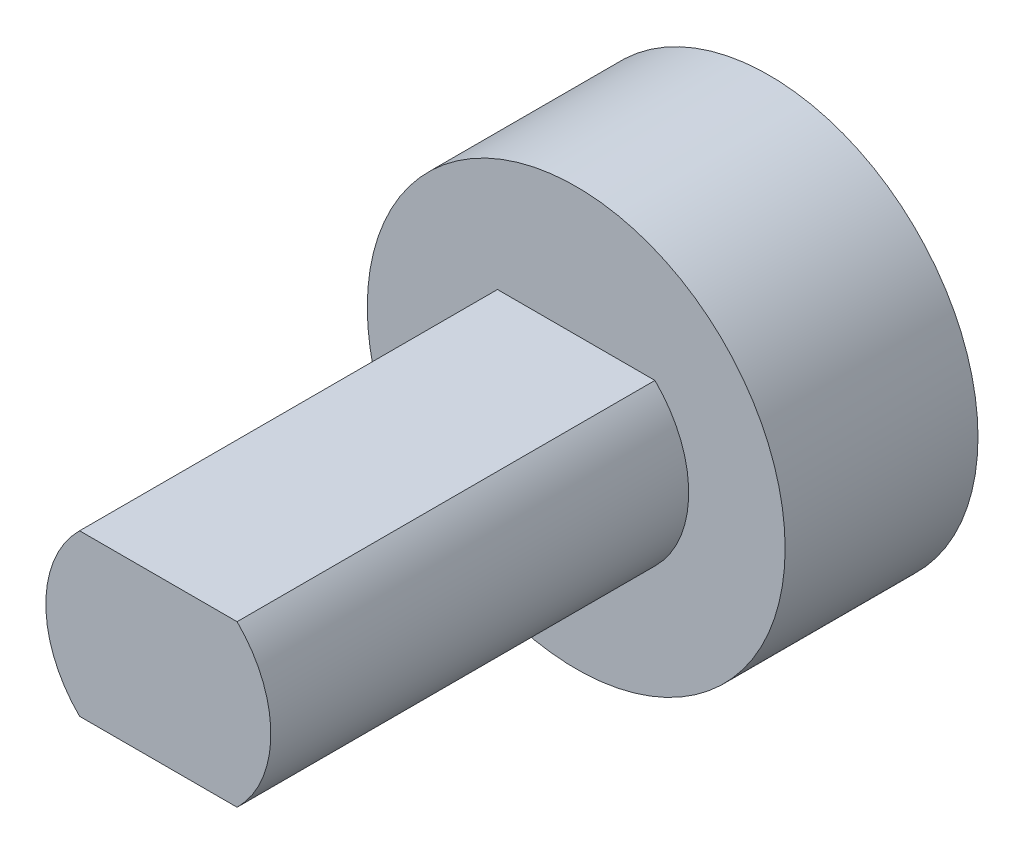
SolidWorks part; units mm, degrees
ref_plane "Front Plane" through (0, 0, 0) normal (0, 0, 1) x (1, 0, 0)
ref_plane "Top Plane" through (0, 0, 0) normal (0, 1, 0) x (1, 0, 0)
ref_plane "Right Plane" through (0, 0, 0) normal (1, 0, 0) x (0, 0, -1)
sketch "Sketch1" plane through (0, 0, 0) normal (0, 0, 1) x (1, 0, 0)
  circle A0 centre (0, 0) radius 6.5
  dimension "D1" = 13
extrude "Boss-Extrude1" add sketch "Sketch1" along normal blind 6
sketch "Sketch2" plane through (0, 0, 6) normal (0, 0, 1) x (1, 0, 0)
  line L1 (-2.4495, 2.5) -> (2.4495, 2.5)
  line L2 (-2.4495, -2.5) -> (2.4495, -2.5)
  arc A0 (-2.4495, 2.5) -> (-2.4495, -2.5) centre (0, 0) ccw
  arc A1 (2.4495, -2.5) -> (2.4495, 2.5) centre (0, 0) ccw
  point P6 (0, 0)
  point P9 (0, 2.5)
  point P12 (0, -2.5)
  dimension "D1" = 7
extrude "Boss-Extrude2" add sketch "Sketch2" along normal blind 13
sketch "Sketch3" plane through (0, 0, 0) normal (0, 0, -1) x (-1, 0, 0)
  circle A0 centre (0, 0) radius 1.5875
  dimension "D1" = 3.175
extrude "Cut-Extrude1" cut sketch "Sketch3" against normal blind 10
